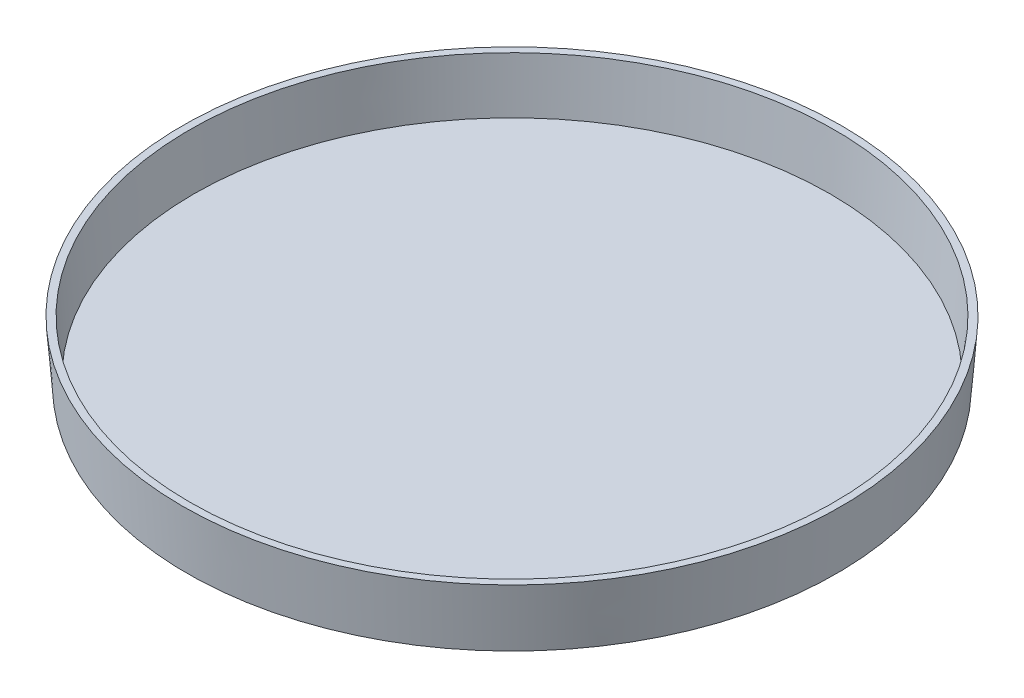
SolidWorks part; units mm, degrees
ref_plane "Front Plane" through (0, 0, 0) normal (0, 0, 1) x (1, 0, 0)
ref_plane "Top Plane" through (0, 0, 0) normal (0, 1, 0) x (1, 0, 0)
ref_plane "Right Plane" through (0, 0, 0) normal (1, 0, 0) x (0, 0, -1)
sketch "Sketch2" plane through (0, 0, 0) normal (0, 0, 1) x (1, 0, 0)
  line L0 (0, 0) -> (46.4185, 0)
  line L1 (0, 0) -> (0, 8.6614) construction
  line L2 (0, 8.6614) -> (47.0916, 8.6614)
  line L3 (46.4185, 0) -> (47.0916, 8.6614)
  line L4 (0, 0) -> (0, 8.6614)
  dimension "D1" = 46.4185
  dimension "D2" = 8.6614
  dimension "D3" = 47.0916
revolve "Revolve1" add sketch "Sketch2" angle 360 about L1
shell "Shell1" thickness 1.016
